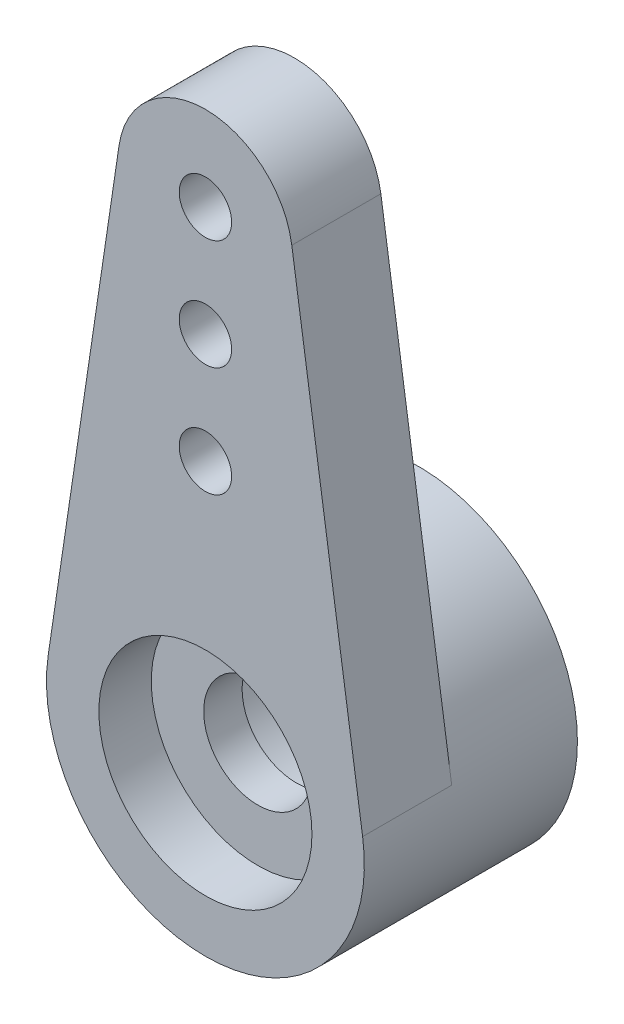
SolidWorks part; units mm, degrees
ref_plane "Plan de face" through (0, 0, 0) normal (0, 0, 1) x (1, 0, 0)
ref_plane "Plan de dessus" through (0, 0, 0) normal (0, 1, 0) x (1, 0, 0)
ref_plane "Plan de droite" through (0, 0, 0) normal (1, 0, 0) x (0, 0, -1)
sketch "Esquisse1" plane through (0, 0, 0) normal (0, 0, 1) x (1, 0, 0)
  line L0 (0, 0) -> (0, 13.95) construction
  line L1 (-4.5006, 0.6686) -> (-2.4729, 14.3174)
  line L2 (4.5006, 0.6686) -> (2.4729, 14.3174)
  arc A0 (-4.5006, 0.6686) -> (4.5006, 0.6686) centre (0, 0) ccw
  arc A1 (-2.4729, 14.3174) -> (2.4729, 14.3174) centre (0, 13.95) cw
  circle A2 centre (0, 7.725) radius 0.75
  circle A3 centre (0, 10.875) radius 0.75
  circle A4 centre (0, 14.025) radius 0.75
  dimension "D1" = 4.55
  dimension "D2" = 13.95
  dimension "D3" = 2.5
  dimension "D4" = 1.5
  dimension "D7" = 3.15
  dimension "D6" = 7.725
  dimension "D5" = 3
extrude "Boss.-Extru.1" add sketch "Esquisse1" along normal blind 2.55
sketch "Esquisse2" plane through (0, 0, 0) normal (0, 0, -1) x (-1, 0, 0)
  circle A0 centre (0, 0) radius 4.55
  arc A1 (-4.5006, 0.6686) -> (4.5006, 0.6686) centre (0, 0) ccw construction
extrude "Boss.-Extru.2" add sketch "Esquisse2" along normal offset from surface (3.55 mm away) 6.1 up to face at (0.75, 10.875, 2.55)
sketch "Esquisse3" plane through (0, 0, 2.55) normal (0, 0, 1) x (1, 0, 0)
  circle A0 centre (0, 0) radius 3.05
  arc A1 (-4.5006, 0.6686) -> (4.5006, 0.6686) centre (0, 0) ccw construction
  dimension "D1" = 6.1
extrude "Enlèv. mat.-Extru.1" cut sketch "Esquisse3" against normal blind 1.5
hole_wizard "Diamètre du perçage Ø3.1 (3.1)1" positions "Esquisse4" profile "Esquisse5" hole size "Ø3.1" standard "ISO" end condition through all
sketch "Esquisse4" plane through (0, 0, 1.05) normal (0, 0, 1) x (1, 0, 0)
  circle A0 centre (0, 0) radius 3.05 construction
  point P0 (0, 0)
sketch "Esquisse5" plane through (0, 0, 1.05) normal (1, 0, 0) x (0, -1, 0)
  line L0 (0, 0) -> (0, 4.6)
  line L1 (0, 4.6) -> (1.55, 4.6)
  line L2 (1.55, 4.6) -> (1.55, 0)
  line L5 (1.55, 0) -> (0, 0)
  line L11 (0, -6.35) -> (0, 107.95) construction
  dimension "Diamètre du perçage jusqu'au prochain" = 3.1
  dimension "Profondeur du perçage jusqu'au prochain" = 4.6
sketch "Esquisse6" plane through (0, 0, -3.55) normal (0, 0, -1) x (-1, 0, 0)
  circle A0 centre (0, 0) radius 2.75
  circle A1 centre (0, 0) radius 4.55 construction
  dimension "D1" = 5.5
extrude "Enlèv. mat.-Extru.2" cut sketch "Esquisse6" against normal blind 3.5
